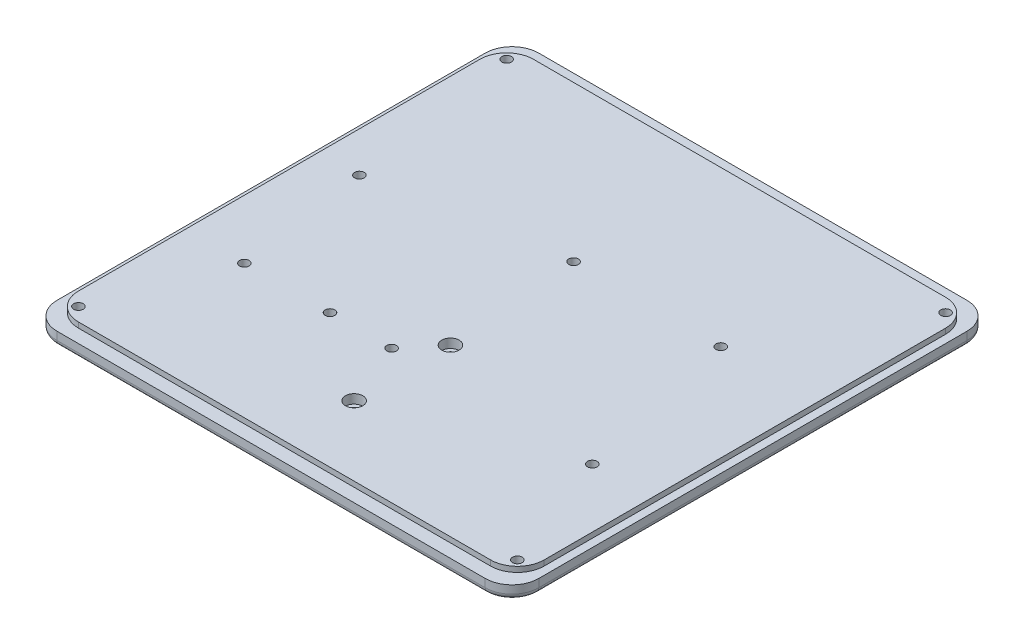
SolidWorks part; units mm, degrees
material "Allzweck-PBT"
ref_plane "Ebene vorne" through (0, 0, 0) normal (0, 0, 1) x (1, 0, 0)
ref_plane "Ebene oben" through (0, 0, 0) normal (0, 1, 0) x (1, 0, 0)
ref_plane "Ebene rechts" through (0, 0, 0) normal (1, 0, 0) x (0, 0, -1)
sketch "Skizze1" plane through (0, 0, 0) normal (0, 1, 0) x (1, 0, 0)
  line L1 (90, 90) -> (-90, 90)
  line L2 (90, 90) -> (90, -90)
  line L3 (90, -90) -> (-90, -90)
  line L4 (-90, 90) -> (-90, -90)
  line L5 (90, 90) -> (-90, -90) construction
  line L6 (90, -90) -> (-90, 90) construction
  point P0 (0, 0)
  dimension "D1" = 180
  dimension "D2" = 180
extrude "Aufsatz-Linear austragen1" add sketch "Skizze1" along normal blind 5 contours L4 L3 L2 L1
sketch "Skizze2" plane through (0, 5, 0) normal (0, 1, 0) x (1, 0, 0)
  line L1 (77, 85) -> (-77, 85)
  line L2 (87, 75) -> (87, -75)
  line L3 (77, -85) -> (-77, -85)
  line L4 (-87, 75) -> (-87, -75)
  line L5 (87, 85) -> (-87, -85) construction
  line L6 (87, -85) -> (-87, 85) construction
  arc A0 (-77, -85) -> (-87, -75) centre (-77, -75) cw
  arc A1 (87, -75) -> (77, -85) centre (77, -75) cw
  arc A2 (77, 85) -> (87, 75) centre (77, 75) cw
  arc A3 (-77, 85) -> (-87, 75) centre (-77, 75) ccw
  point P0 (0, 0)
  dimension "D1" = 10
  dimension "176" = 174
  dimension "D2" = 170
extrude "Aufsatz-Linear austragen2" add sketch "Skizze2" along normal blind 2
hole_wizard "Stirnsenkung für M3 Zylinderschraube mit Innensechskant1" positions "Skizze5" profile "Skizze6" counterbore size "M3" standard "DIN"
sketch "Skizze5" plane through (0, 7, 0) normal (0, 1, 0) x (1, 0, 0)
  line L0 (0, 85) -> (0, -85) construction
  line L1 (77, 85) -> (-77, 85) construction
  line L2 (-77, -85) -> (77, -85) construction
  line L5 (-77, -85) -> (77, -85) construction
  point P0 (0, -23)
  point P2 (0, -59)
  point P25 (0, 0)
  point P26 (0, 0)
  dimension "D1" = 26
  dimension "D4" = 36
sketch "Skizze6" plane through (0, 7, 23) normal (1, 0, 0) x (0, 0, 1)
  line L0 (0, 0) -> (0, 10.1815)
  line L1 (0, 10.1815) -> (1.8, 9.1)
  line L2 (1.8, 9.1) -> (1.8, 3.4)
  line L3 (1.8, 3.4) -> (3.25, 3.4)
  line L4 (3.25, 3.4) -> (3.25, 0)
  line L5 (3.25, 0) -> (0, 0)
  line L10 (0, 10.1815) -> (-1.8, 9.1) construction
  line L11 (0, -6.35) -> (0, 107.95) construction
  dimension "Bohrerdurchmesser" = 3.6
  dimension "Bohrungstiefe" = 9.1
  dimension "Senkdurchmesser2" = 6.5
  dimension "Senktiefe2" = 3.4
  dimension "Spitzenwinkel" = 118
hole_wizard "Stirnsenkung für M3 Zylinderschraube mit Innensechskant2" positions "Skizze7" profile "Skizze8" counterbore size "M3" standard "DIN"
sketch "Skizze7" plane through (0, 0, 0) normal (0, -1, 0) x (-1, 0, 0)
  line L0 (-77, 85) -> (77, 85) construction
  line L1 (-87, -75) -> (-87, 75) construction
  line L2 (-77, 85) -> (77, 85) construction
  line L3 (87, 75) -> (87, -75) construction
  line L4 (77, -85) -> (-77, -85) construction
  point P0 (-82, 80)
  point P2 (82, 80)
  point P4 (82, -80)
  point P6 (-82, -80)
  dimension "D1" = 5
  dimension "D2" = 5
  dimension "D3" = 5
  dimension "D4" = 5
  dimension "D5" = 5
  dimension "D6" = 5
  dimension "D7" = 5
  dimension "5" = 5
sketch "Skizze8" plane through (82, 0, -80) normal (1, 0, 0) x (0, 0, -1)
  line L0 (0, 0) -> (0, 10.1815)
  line L1 (0, 10.1815) -> (1.8, 9.1)
  line L2 (1.8, 9.1) -> (1.8, 3.4)
  line L3 (1.8, 3.4) -> (3.25, 3.4)
  line L4 (3.25, 3.4) -> (3.25, 0)
  line L5 (3.25, 0) -> (0, 0)
  line L10 (0, 10.1815) -> (-1.8, 9.1) construction
  line L11 (0, -6.35) -> (0, 107.95) construction
  dimension "Bohrerdurchmesser" = 3.6
  dimension "Bohrungstiefe" = 9.1
  dimension "Senkdurchmesser2" = 6.5
  dimension "Senktiefe2" = 3.4
  dimension "Spitzenwinkel" = 118
fillet "Verrundung1" radius 10 4 edges at (90, 2.5, -90) (90, 2.5, 90) (-90, 2.5, 90) (-90, 2.5, -90)
fillet "Verrundung2" radius 2 8 edges at (-87.0711, 0, -87.0711) (0, 0, -90) (87.0711, 0, -87.0711) (90, 0, 0) (87.0711, 0, 87.0711) (0, 0, 90) (-87.0711, 0, 87.0711) (-90, 0, 0)
hole_wizard "Stirnsenkung für M3 Zylinderschraube mit Innensechskant3" positions "Skizze9" profile "Skizze10" counterbore size "M3" standard "DIN" end condition through all
sketch "Skizze9" plane through (0, 0, 0) normal (0, -1, 0) x (-1, 0, 0)
  line L1 (-77, 85) -> (77, 85) construction
  line L2 (-87, -75) -> (-87, 75) construction
  line L3 (70.8826, -35) -> (-74.3113, -35) construction
  line L5 (87, 75) -> (87, -75) construction
  line L6 (-87, -75) -> (-87, 75) construction
  line L7 (77, -85) -> (-77, -85) construction
  line L8 (-77, 85) -> (77, 85) construction
  point P0 (-51, 27)
  point P2 (4, 27)
  point P4 (-65, -35)
  point P6 (10, -35)
  point P8 (33, -35)
  point P10 (65, -35)
  point P12 (72, 15)
  dimension "D1" = 55
  dimension "D2" = 58
  dimension "D3" = 36
  dimension "D4" = 32
  dimension "D5" = 75
  dimension "D6" = 22
  dimension "D7" = 22
  dimension "D8" = 50
  dimension "D9" = 15
  dimension "D10" = 70
sketch "Skizze10" plane through (51, 0, -27) normal (1, 0, 0) x (0, 0, -1)
  line L0 (0, 0) -> (0, 7)
  line L1 (0, 7) -> (1.8, 7)
  line L3 (1.8, 7) -> (1.8, 3.4)
  line L4 (1.8, 3.4) -> (3.25, 3.4)
  line L5 (3.25, 3.4) -> (3.25, 0)
  line L7 (3.25, 0) -> (0, 0)
  line L11 (0, -6.35) -> (0, 107.95) construction
  dimension "Bohrerdurchmesser" = 3.6
  dimension "Bohrungstiefe" = 7
  dimension "Senkdurchmesser2" = 6.5
  dimension "Senktiefe2" = 3.4
